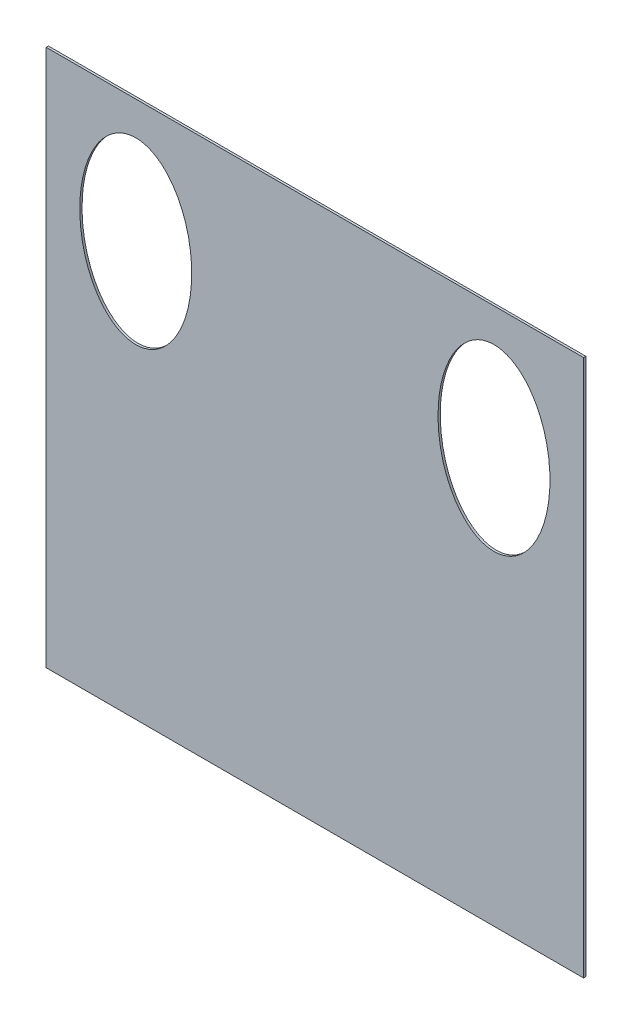
SolidWorks part; units mm, degrees
material "PVC Rigid"
ref_plane "Front Plane" through (0, 0, 0) normal (0, 0, 1) x (1, 0, 0)
ref_plane "Top Plane" through (0, 0, 0) normal (0, 1, 0) x (1, 0, 0)
ref_plane "Right Plane" through (0, 0, 0) normal (1, 0, 0) x (0, 0, -1)
sketch "Sketch1" plane through (0, 0, 0) normal (0, 0, 1) x (1, 0, 0)
  line L1 (-183.8876, 299.1322) -> (425.7124, 299.1322)
  line L2 (-183.8876, 299.1322) -> (-183.8876, -310.4678)
  line L3 (-183.8876, -310.4678) -> (425.7124, -310.4678)
  line L4 (425.7124, 299.1322) -> (425.7124, -310.4678)
  dimension "D1" = 609.6
  dimension "D2" = 609.6
extrude "Boss-Extrude1" add sketch "Sketch1" along normal blind 2.54
sketch "Sketch2" plane through (0, 0, 2.54) normal (0, 0, 1) x (1, 0, 0)
  line L0 (120.9124, 299.1322) -> (120.9124, -310.4678) construction
  line L1 (425.7124, 299.1322) -> (-183.8876, 299.1322) construction
  line L2 (-183.8876, -310.4678) -> (425.7124, -310.4678) construction
  line L3 (-183.8876, 299.1322) -> (-183.8876, -310.4678) construction
  ellipse E0 centre (-82.2876, 159.4322) end of major axis (-82.2876, 57.8322) minor radius 63.5
  ellipse E1 centre (324.1124, 159.4322) end of major axis (324.1124, 57.8322) minor radius 63.5
  point P12 (-69.3742, 164.9819)
  dimension "D1" = 203.2
  dimension "D2" = 127
  dimension "D3" = 101.6
  dimension "D4" = 139.7
extrude "Cut-Extrude1" cut sketch "Sketch2" against normal through all
